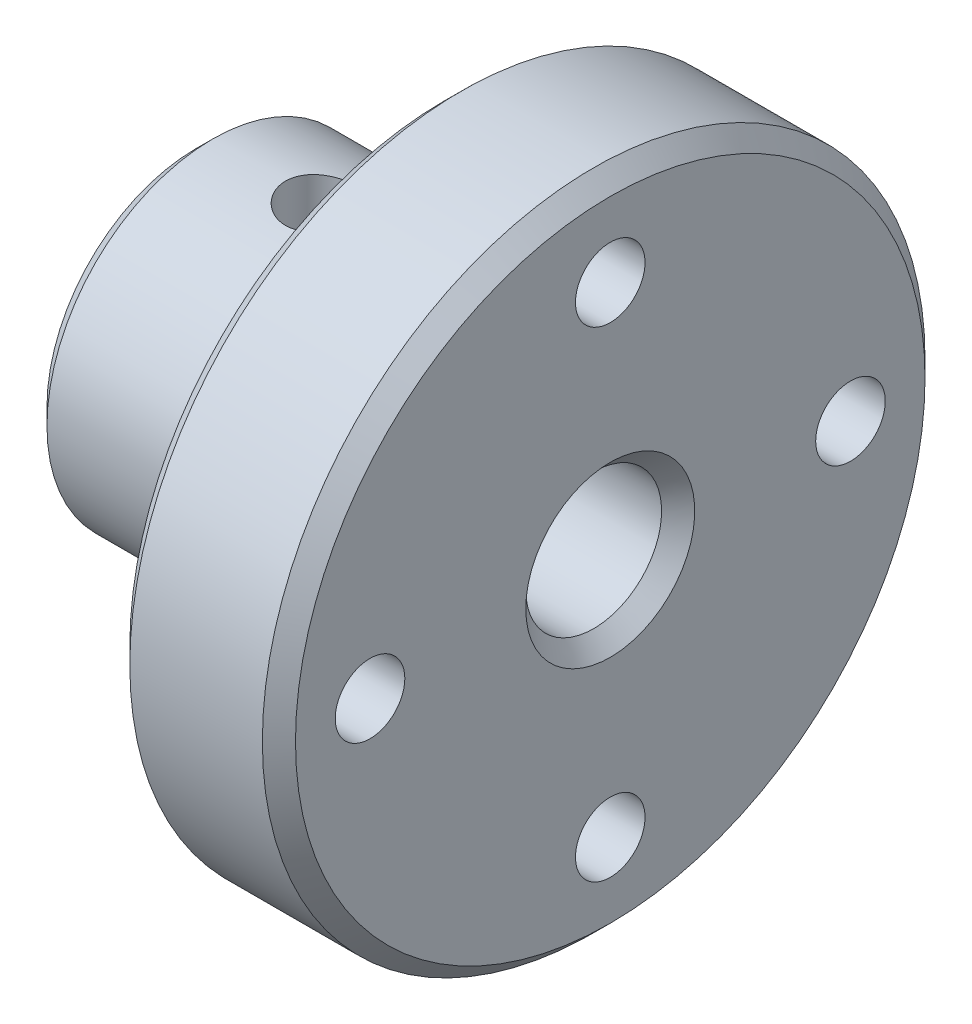
SolidWorks part; units mm, degrees
material "6061-T6 (SS)"
ref_plane "Front Plane" through (0, 0, 0) normal (0, 0, 1) x (1, 0, 0)
ref_plane "Top Plane" through (0, 0, 0) normal (0, 1, 0) x (1, 0, 0)
ref_plane "Right Plane" through (0, 0, 0) normal (1, 0, 0) x (0, 0, -1)
sketch "Sketch1" plane through (0, 0, 0) normal (0, 0, 1) x (1, 0, 0)
  line L0 (0, 4.1) -> (0, 10)
  line L1 (0, 10) -> (15, 10)
  line L2 (15, 10) -> (15, 20)
  line L3 (15, 20) -> (25, 20)
  line L4 (25, 20) -> (25, 4.1)
  line L5 (25, 4.1) -> (0, 4.1)
  line L6 (0, 0) -> (42.5818, 0) construction
  dimension "D1" = 25
  dimension "D2" = 8.2
  dimension "D3" = 20
  dimension "D4" = 40
  dimension "D5" = 10
revolve "Revolve1" add sketch "Sketch1" angle 360 about L6
hole_wizard "M5x0.8 Tapped Hole1" positions "Sketch3" profile "Sketch2" tap size "M5x0.8" standard "ANSI Metric" end condition through all
sketch "Sketch3" plane through (25, 0, 0) normal (1, 0, 0) x (0, 0, -1)
  line L0 (-14.5, 0) -> (0, 0) construction
  point P1 (-14.5, 0)
  dimension "D1" = 14.5
sketch "Sketch2" plane through (25, 0, 14.5) normal (0, 1, 0) x (0, 0, -1)
  line L0 (0, 0) -> (0, 25)
  line L1 (0, 25) -> (2.1, 25)
  line L2 (2.1, 25) -> (2.1, 0)
  line L5 (2.1, 0) -> (0, 0)
  line L11 (0, -6.35) -> (0, 107.95) construction
  dimension "Thread Major Dia." = 4.2
  dimension "Thru Tap Drill Depth" = 25
pattern_circular "CirPattern1" count 4 over 360 about axis through (0, 0, 0) along (1, 0, 0) of "M5x0.8 Tapped Hole1"
hole_wizard "M5x0.8 Tapped Hole2" positions "Sketch7" profile "Sketch6" tap size "M5x0.8" standard "ANSI Metric"
sketch "Sketch7" plane through (0, 0, 0) normal (0, 1, 0) x (1, 0, 0)
  line L0 (0, 10) -> (0, -10) construction
  point P0 (7.5, 0)
  dimension "D1" = 7.5
sketch "Sketch6" plane through (7.5, 0, 0) normal (1, 0, 0) x (0, 0, -1)
  line L0 (0, 0) -> (0, 20)
  line L1 (0, 20) -> (2.1, 20)
  line L2 (2.1, 20) -> (2.1, 0)
  line L5 (2.1, 0) -> (0, 0)
  line L11 (0, -6.35) -> (0, 107.95) construction
  dimension "Thread Major Dia." = 4.2
  dimension "Thru Tap Drill Depth" = 20
pattern_circular "CirPattern2" count 2 over 90 about axis through (25, 0, 0) along (-1, 0, 0) of "M5x0.8 Tapped Hole2"
chamfer "Chamfer1" distance 1 angle 45 5 edges at (0, 0, 4.1) (25, 0, 4.1) (25, 0, 20) (15, 0, 20) (0, 0, 10)
